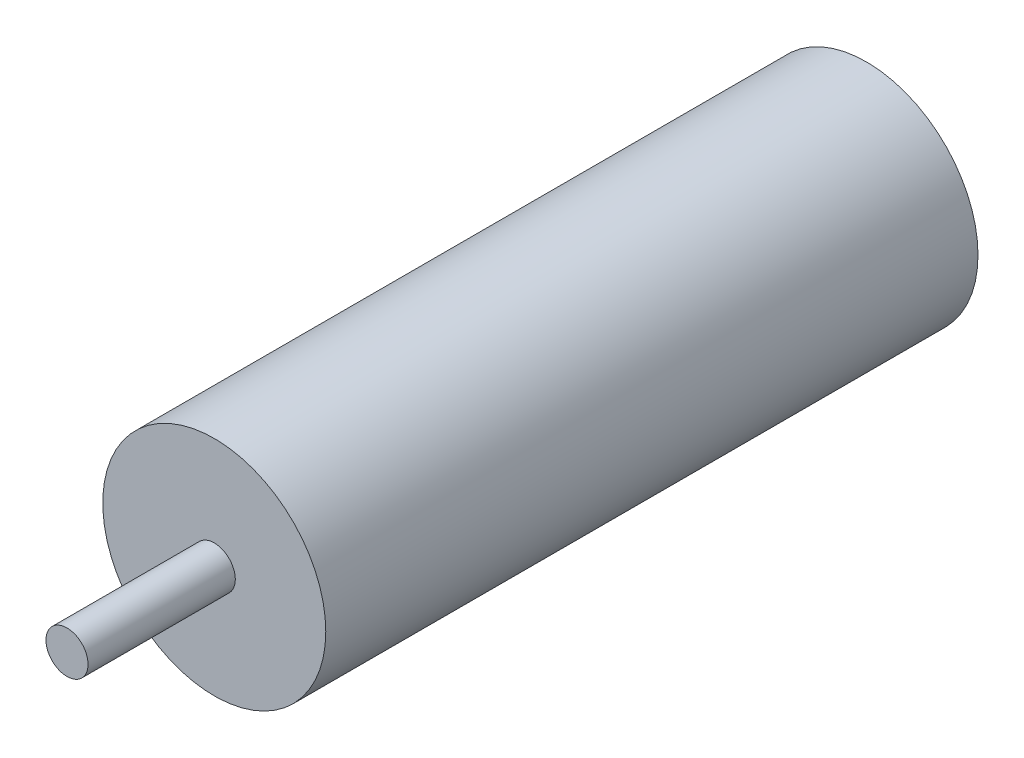
SolidWorks part; units mm, degrees
material "1060 Alloy"
ref_plane "Front Plane" through (0, 0, 0) normal (0, 0, 1) x (1, 0, 0)
ref_plane "Top Plane" through (0, 0, 0) normal (0, 1, 0) x (1, 0, 0)
ref_plane "Right Plane" through (0, 0, 0) normal (1, 0, 0) x (0, 0, -1)
sketch "Sketch1" plane through (0, 0, 0) normal (0, 0, 1) x (1, 0, 0)
  circle A0 centre (0, 0) radius 5.3
  dimension "D1" = 10.6
extrude "Extrude1" add sketch "Sketch1" along normal blind 31
sketch "Sketch2" plane through (0, 0, 31) normal (0, 0, 1) x (1, 0, 0)
  circle A0 centre (0, 0) radius 1
  dimension "D1" = 2
extrude "Extrude2" add sketch "Sketch2" along normal blind 7
